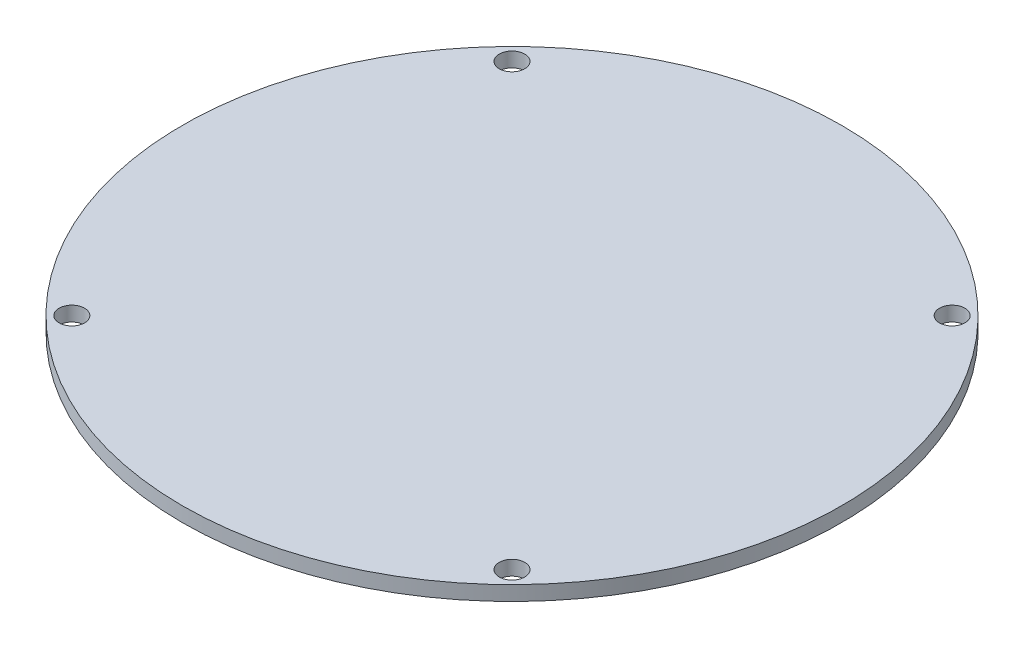
SolidWorks part; units mm, degrees
ref_plane "Front Plane" through (0, 0, 0) normal (0, 0, 1) x (1, 0, 0)
ref_plane "Top Plane" through (0, 0, 0) normal (0, 1, 0) x (1, 0, 0)
ref_plane "Right Plane" through (0, 0, 0) normal (1, 0, 0) x (0, 0, -1)
sketch "Sketch1" plane through (0, 0, 0) normal (0, 1, 0) x (1, 0, 0)
  circle A0 centre (0, 0) radius 57.15
  dimension "D1" = 114.3
extrude "Boss-Extrude1" add sketch "Sketch1" along normal blind 2.54
sketch "Sketch2" plane through (0, 2.54, 0) normal (0, 1, 0) x (1, 0, 0)
  line L1 (38.1661, -38.1661) -> (-38.1661, -38.1661) construction
  line L2 (38.1661, -38.1661) -> (38.1661, 38.1661) construction
  line L3 (38.1661, 38.1661) -> (-38.1661, 38.1661) construction
  line L4 (-38.1661, -38.1661) -> (-38.1661, 38.1661) construction
  line L5 (38.1661, -38.1661) -> (-38.1661, 38.1661) construction
  line L6 (38.1661, 38.1661) -> (-38.1661, -38.1661) construction
  circle A0 centre (-38.1661, 38.1661) radius 2.2108
  circle A1 centre (38.1661, 38.1661) radius 2.2108
  circle A2 centre (38.1661, -38.1661) radius 2.2108
  circle A3 centre (-38.1661, -38.1661) radius 2.2108
  point P0 (0, 0)
  dimension "D1" = 107.95
extrude "Cut-Extrude1" cut sketch "Sketch2" against normal through all
